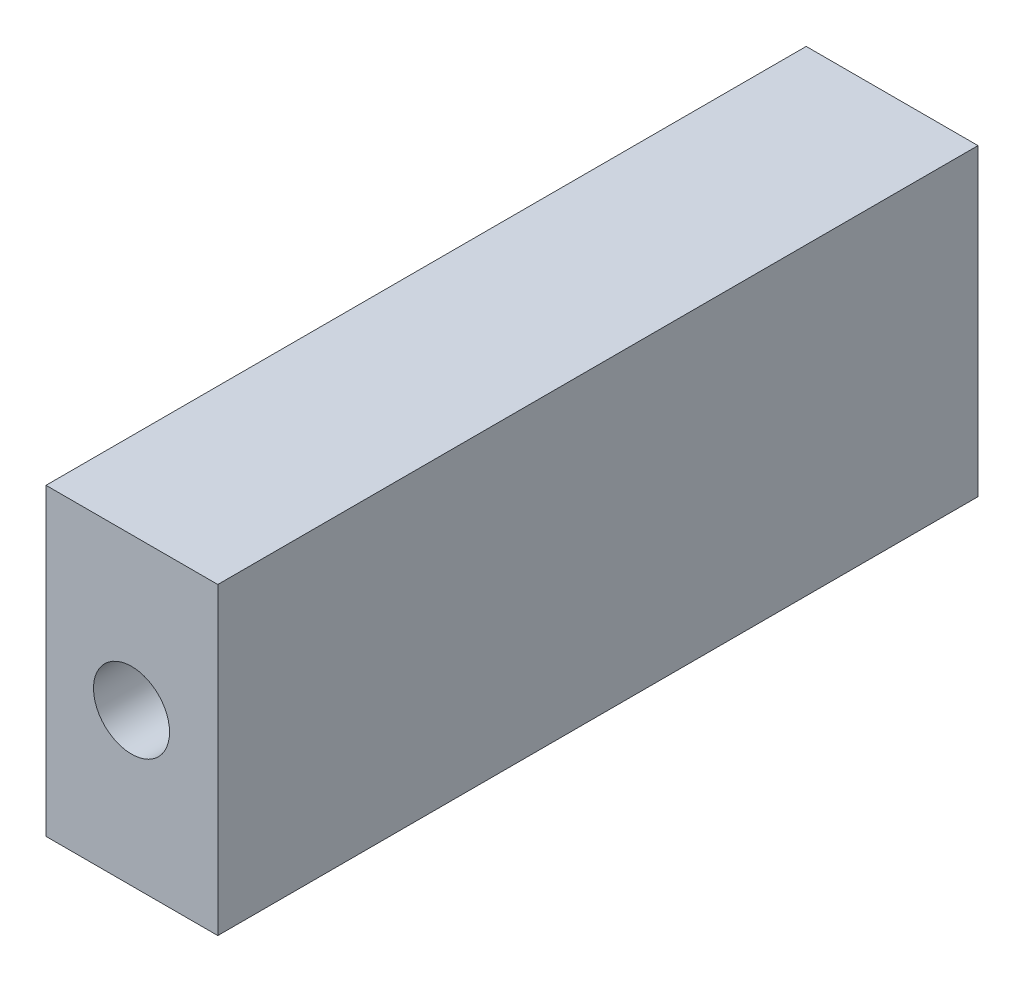
SolidWorks part; units mm, degrees
ref_plane "Front Plane" through (0, 0, 0) normal (0, 0, 1) x (1, 0, 0)
ref_plane "Top Plane" through (0, 0, 0) normal (0, 1, 0) x (1, 0, 0)
ref_plane "Right Plane" through (0, 0, 0) normal (1, 0, 0) x (0, 0, -1)
sketch "Sketch2" plane through (0, 0, 0) normal (0, 0, 1) x (1, 0, 0)
  line L1 (0, 0) -> (2.26, 0)
  line L2 (0, 0) -> (0, 4)
  line L3 (0, 4) -> (2.26, 4)
  line L4 (2.26, 0) -> (2.26, 4)
  dimension "D1" = 2.26
  dimension "D2" = 4
extrude "Boss-Extrude1" add sketch "Sketch2" along normal blind 10
sketch "Sketch3" plane through (0, 0, 10) normal (0, 0, 1) x (1, 0, 0)
  line L0 (0, 2) -> (2.26, 2) construction
  line L1 (0, 4) -> (0, 0) construction
  line L2 (2.26, 0) -> (2.26, 4) construction
  line L3 (0, 2) -> (2.26, 2) construction
  line L4 (2.26, 4) -> (0, 4) construction
  line L5 (0, 0) -> (2.26, 0) construction
  line L6 (1.125, 4) -> (1.125, 0) construction
  circle A0 centre (1.125, 2) radius 0.5
  dimension "D1" = 1
  dimension "D2" = 2
  dimension "D3" = 1.125
extrude "Cut-Extrude1" cut sketch "Sketch3" against normal blind 5
sketch "Sketch4" plane through (0, 0, 10) normal (0, 0, 1) x (1, 0, 0)
  point P0 (1.125, 2)
  point P3 (0, 0)
  point P9 (0, 0)
  point P11 (0, 0)
  point P13 (0, 0)
  point P15 (0, 0)
  point P17 (0, 0)
  point P27 (0, 0)
  point P37 (0, 0)
